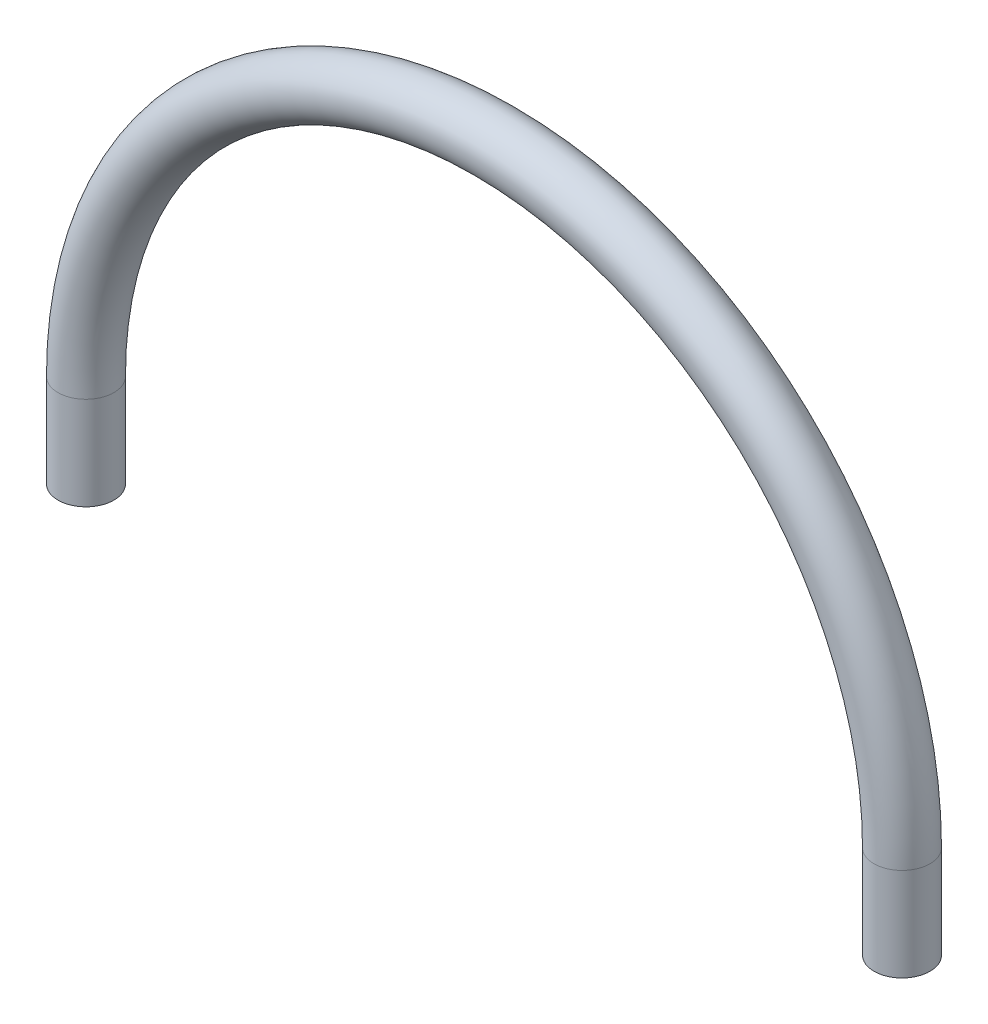
SolidWorks part; units mm, degrees
ref_plane "Front Plane" through (0, 0, 0) normal (0, 0, 1) x (1, 0, 0)
ref_plane "Top Plane" through (0, 0, 0) normal (0, 1, 0) x (1, 0, 0)
ref_plane "Right Plane" through (0, 0, 0) normal (1, 0, 0) x (0, 0, -1)
sketch "Sketch2" plane through (0, 0, 0) normal (0, 0, 1) x (1, 0, 0)
  line L0 (0, 42.9196) -> (0, -45.7432) construction
  line L1 (-55.626, 0) -> (-55.626, -12.7)
  line L2 (55.626, 0) -> (55.626, -12.7)
  arc A0 (-55.626, 0) -> (55.626, 0) centre (0, 0) cw
  point P8 (0, 0)
  dimension "D1" = 111.252
  dimension "D2" = 12.7
sweep "Sweep1" add path "Sketch2" circular profile diameter 7.62 parameters "D3"=7.62
